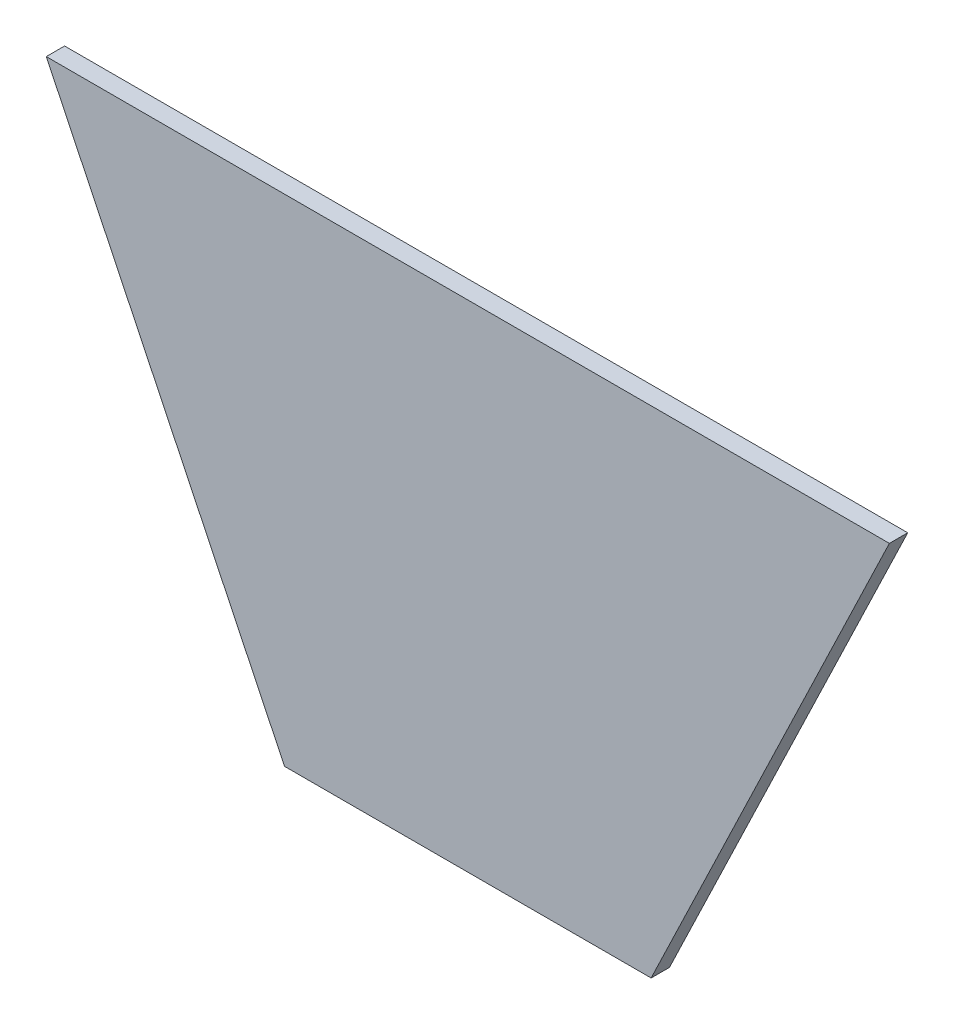
SolidWorks part; units mm, degrees
ref_plane "Front Plane" through (0, 0, 0) normal (0, 0, 1) x (1, 0, 0)
ref_plane "Top Plane" through (0, 0, 0) normal (0, 1, 0) x (1, 0, 0)
ref_plane "Right Plane" through (0, 0, 0) normal (1, 0, 0) x (0, 0, -1)
sketch "Sketch1" plane through (0, 0, 0) normal (0, 0, 1) x (1, 0, 0)
  line L0 (-100, 0) -> (100, 0)
  line L1 (100, 0) -> (230, 270.3701)
  line L2 (230, 270.3701) -> (-230, 270.3701)
  line L3 (-230, 270.3701) -> (-100, 0)
  point P3 (0, 0)
  dimension "D1" = 200
  dimension "D2" = 460
  dimension "D3" = 300
  dimension "D4" = 300
extrude "Boss-Extrude1" add sketch "Sketch1" along normal blind 10
